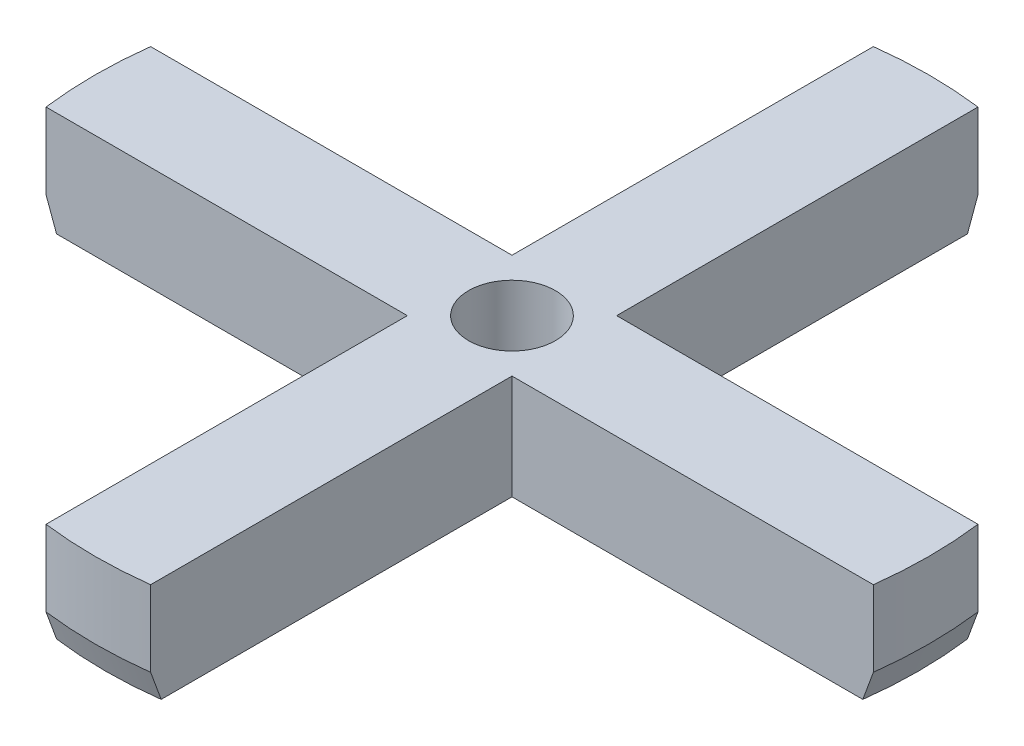
SolidWorks part; units mm, degrees
ref_plane "Спереди" through (0, 0, 0) normal (0, 0, 1) x (1, 0, 0)
ref_plane "Сверху" through (0, 0, 0) normal (0, 1, 0) x (1, 0, 0)
ref_plane "Справа" through (0, 0, 0) normal (1, 0, 0) x (0, 0, -1)
sketch "Sketch1" plane through (0, 0, 0) normal (0, 1, 0) x (1, 0, 0)
  line L0 (-39.5351, 5) -> (-5, 5)
  line L1 (5, -39.5351) -> (-5, -39.5351) construction
  line L2 (5, -39.5351) -> (5, 39.5351) construction
  line L3 (5, 39.5351) -> (-5, 39.5351) construction
  line L4 (-5, -39.5351) -> (-5, 39.5351) construction
  line L5 (5, -39.5351) -> (-5, 39.5351) construction
  line L6 (5, 39.5351) -> (-5, -39.5351) construction
  line L7 (39.5351, -5) -> (-39.5351, -5) construction
  line L8 (39.5351, -5) -> (39.5351, 5) construction
  line L9 (39.5351, 5) -> (-39.5351, 5) construction
  line L10 (-39.5351, -5) -> (-39.5351, 5) construction
  line L11 (39.5351, -5) -> (-39.5351, 5) construction
  line L12 (39.5351, 5) -> (-39.5351, -5) construction
  line L13 (-5, 5) -> (-5, 39.5351)
  line L14 (5, 39.5351) -> (5, 5)
  line L15 (5, 5) -> (39.5351, 5)
  line L16 (39.5351, -5) -> (5, -5)
  line L17 (5, -5) -> (5, -39.5351)
  line L18 (-5, -39.5351) -> (-5, -5)
  line L19 (-5, -5) -> (-39.5351, -5)
  circle A0 centre (0, 0) radius 39.85 construction
  circle A1 centre (0, 0) radius 4.15
  arc A2 (-5, 39.5351) -> (5, 39.5351) centre (0, 0) cw
  arc A3 (39.5351, -5) -> (39.5351, 5) centre (0, 0) ccw
  arc A4 (-39.5351, -5) -> (-39.5351, 5) centre (0, 0) cw
  arc A5 (-5, -39.5351) -> (5, -39.5351) centre (0, 0) ccw
  dimension "D1" = 79.7
  dimension "D2" = 8.3
  dimension "D3" = 10
extrude "Boss-Extrude1" add sketch "Sketch1" along normal blind 10
chamfer "Chamfer1" distance 1 angle 70 4 edges at (-39.85, 0, 0) (0, 0, -39.85) (39.85, 0, 0) (0, 0, 39.85)
